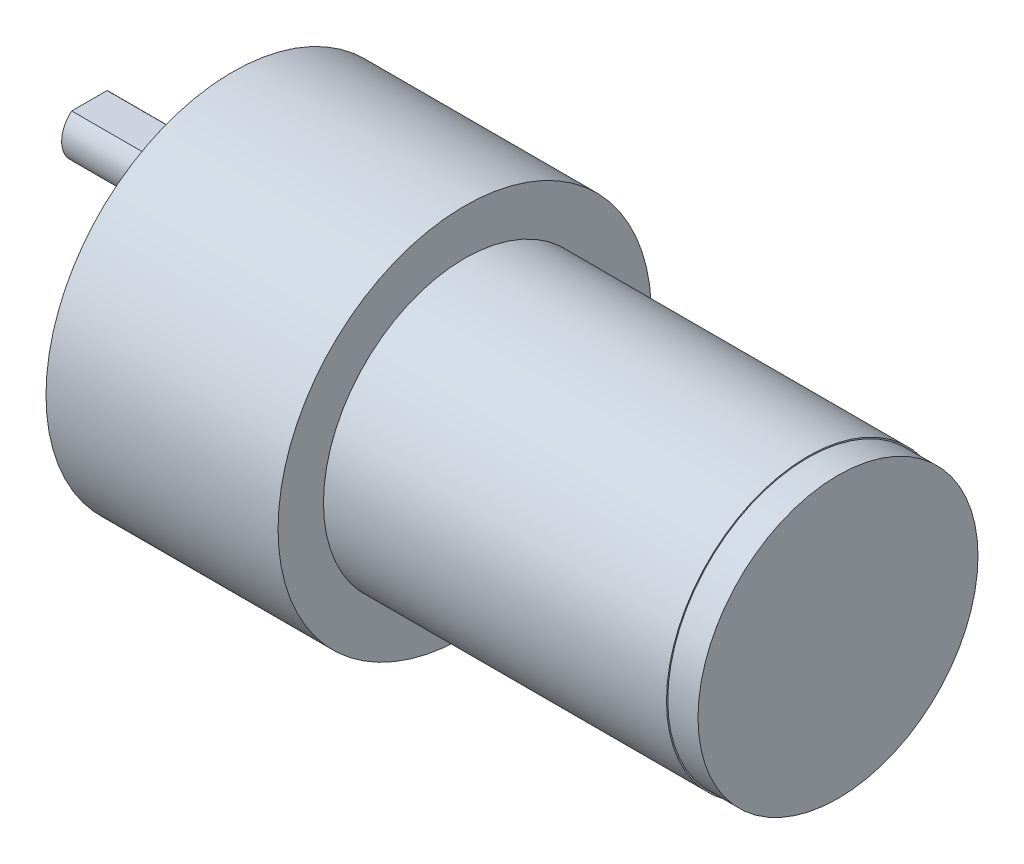
SolidWorks part; units mm, degrees
ref_plane "Front Plane" through (0, 0, 0) normal (0, 0, 1) x (1, 0, 0)
ref_plane "Top Plane" through (0, 0, 0) normal (0, 1, 0) x (1, 0, 0)
ref_plane "Right Plane" through (0, 0, 0) normal (1, 0, 0) x (0, 0, -1)
sketch "Sketch1" plane through (0, 0, 0) normal (1, 0, 0) x (0, 0, -1)
  circle A0 centre (0, 0) radius 14
  dimension "D1" = 28
extrude "Boss-Extrude1" add sketch "Sketch1" against normal blind 34
sketch "Sketch2" plane through (-34, 0, 0) normal (-1, 0, 0) x (0, 0, 1)
  circle A0 centre (0, 0) radius 18.5
  dimension "D1" = 37
extrude "Boss-Extrude2" add sketch "Sketch2" along normal blind 23
sketch "Sketch3" plane through (-57, 0, 0) normal (-1, 0, 0) x (0, 0, 1)
  circle A0 centre (-6.8, 0) radius 6
  dimension "D1" = 12
  dimension "D2" = 6.8
extrude "Boss-Extrude3" add sketch "Sketch3" along normal blind 6
sketch "Sketch5" plane through (-63, 0, 0) normal (-1, 0, 0) x (0, 0, 1)
  circle A0 centre (-6.8, 0) radius 2.75
  dimension "D1" = 5.5
extrude "Boss-Extrude4" add sketch "Sketch5" along normal blind 15
sketch "Sketch6" plane through (-78, 0, 0) normal (-1, 0, 0) x (0, 0, 1)
  line L0 (-8.55, 2.1213) -> (-5.05, 2.1213)
  arc A0 (-5.05, 2.1213) -> (-8.55, 2.1213) centre (-6.8, 0) ccw
  dimension "D1" = 5.5
  dimension "D2" = 3.5
extrude "Cut-Extrude1" cut sketch "Sketch6" against normal blind 12
sketch "Sketch7" plane through (0, 0, 0) normal (1, 0, 0) x (0, 0, -1)
  circle A0 centre (0, 0) radius 13.875
  dimension "D1" = 27.75
extrude "Boss-Extrude5" add sketch "Sketch7" along normal blind 3
